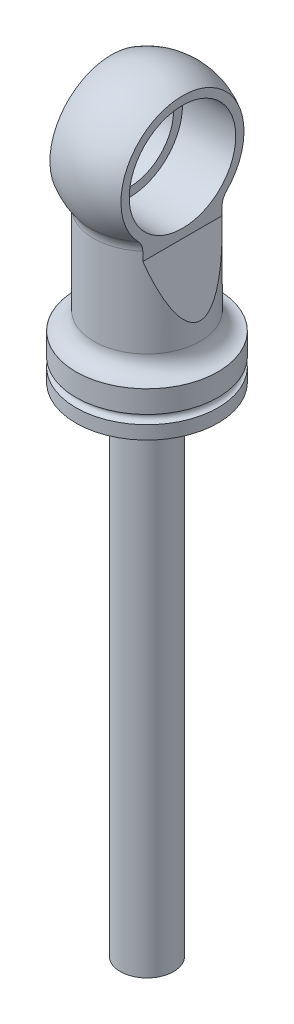
SolidWorks part; units mm, degrees
material "6061 Alloy"
ref_plane "Front" through (0, 0, 0) normal (0, 0, 1) x (1, 0, 0)
ref_plane "Top" through (0, 0, 0) normal (0, 1, 0) x (1, 0, 0)
ref_plane "Right" through (0, 0, 0) normal (1, 0, 0) x (0, 0, -1)
sketch "Sketch1" plane through (0, 0, 0) normal (0, 0, 1) x (1, 0, 0)
  line L0 (0, 29.5686) -> (0, -41.1714) construction
  line L1 (-9.525, -9.5165) -> (-9.525, -25.4254)
  line L2 (-12.7, -34.1313) -> (-12.7, -36.5125)
  line L3 (0, 12.7) -> (0, -36.5125)
  line L4 (-12.6746, -28.575) -> (-12.7, -28.575)
  line L5 (-12.7, -28.575) -> (-12.7, -32.5437)
  line L6 (-12.7, -36.5125) -> (0, -36.5125)
  arc A0 (0, 12.7) -> (-10.1559, -7.6254) centre (0, 0) ccw
  arc A1 (-12.6746, -28.575) -> (-9.525, -25.4254) centre (-12.6746, -25.4254) ccw
  arc A2 (-12.7, -34.1313) -> (-12.7, -32.5437) centre (-12.7, -33.3375) ccw
  arc A3 (-9.525, -9.5165) -> (-10.1559, -7.6254) centre (-12.6746, -9.5165) ccw
  dimension "D1" = 25.4
  dimension "D3" = 36.5125
  dimension "D6" = 3.1496
  dimension "D7" = 1.5875
  dimension "D8" = 3.175
  dimension "D9" = 3.1496
  dimension "D2" = 9.525
  dimension "D4" = 12.7
  dimension "D5" = 7.9375
revolve "Revolve1" add sketch "Sketch1" angle 360 about L0
sketch "Sketch2" plane through (0, 0, 0) normal (0, 0, 1) x (1, 0, 0)
  line L0 (-6.35, 10.9985) -> (-6.35, -11.1125)
  line L1 (-6.35, -11.1125) -> (-9.525, -22.225)
  line L2 (-9.525, -9.5165) -> (-9.525, -25.4254) construction
  line L3 (0, 13.8018) -> (0, -5.645) construction
  line L4 (6.35, -11.1125) -> (9.525, -22.225)
  line L5 (6.35, 10.9985) -> (6.35, -11.1125)
  line L6 (-12.7, -36.5125) -> (12.7, -36.5125) construction
  line L7 (-9.525, -22.225) -> (-17.4613, -22.225)
  line L8 (-17.4613, -22.225) -> (-17.4613, 15.4224)
  line L9 (-17.4613, 15.4224) -> (17.4613, 15.4224)
  line L10 (-6.35, 10.9985) -> (-6.35, 13.9933)
  line L11 (-6.35, 13.9933) -> (6.35, 13.9933)
  line L12 (17.4613, -22.225) -> (17.4613, 15.4224)
  line L13 (9.525, -22.225) -> (17.4613, -22.225)
  line L14 (6.35, -11.1125) -> (9.525, -22.225)
  line L15 (6.35, 10.9985) -> (6.35, 13.9933)
  line L16 (6.35, 10.9985) -> (6.35, -11.1125)
  arc A0 (10.1559, -7.6254) -> (-10.1559, -7.6254) centre (0, 0) ccw construction
  point P21 (0, 15.4224)
  point P24 (0, 13.9933)
  dimension "D2" = 11.1125
  dimension "D1" = 12.7
  dimension "D3" = 14.2875
extrude "Extrude1" cut sketch "Sketch2" against normal through all and the other way through all contours L3 L9 L8 L7 L1 L0 L10 L11 | L9 L3 L11 L15 L5 L4 L13 L12
sketch "Sketch4" plane through (0, 0, 0) normal (1, 0, 0) x (0, 0, -1)
  circle A0 centre (0, 0) radius 7.9375
  dimension "D1" = 15.875
extrude "Extrude3" cut sketch "Sketch4" against normal through all and the other way through all
ref_plane "Plane1" through (-3.175, 0, 0) normal (-1, 0, 0) x (0, 0, 1)
sketch "Sketch5" plane through (-3.175, 0, 0) normal (-1, 0, 0) x (0, 0, 1)
  circle A0 centre (0, 0) radius 9.525
  dimension "D1" = 19.05
extrude "Extrude4" cut sketch "Sketch5" against normal through all
sketch "Sketch6" plane through (0, -36.5125, 0) normal (0, -1, 0) x (1, 0, 0)
  circle A0 centre (0, 0) radius 4.7625
  dimension "D1" = 9.525
extrude "Extrude5" add sketch "Sketch6" along normal blind 88.9
sketch3d "3DSketch1"
  line L0 (-6.35, 0, 0) -> (6.35, 0, 0)
  line L1 (-6.35, 0, 0) -> (-3.175, 0, 0) construction
  line L2 (6.35, 0, 0) -> (-3.175, 0, 0) construction
  point P6 (0, 0, 0)
